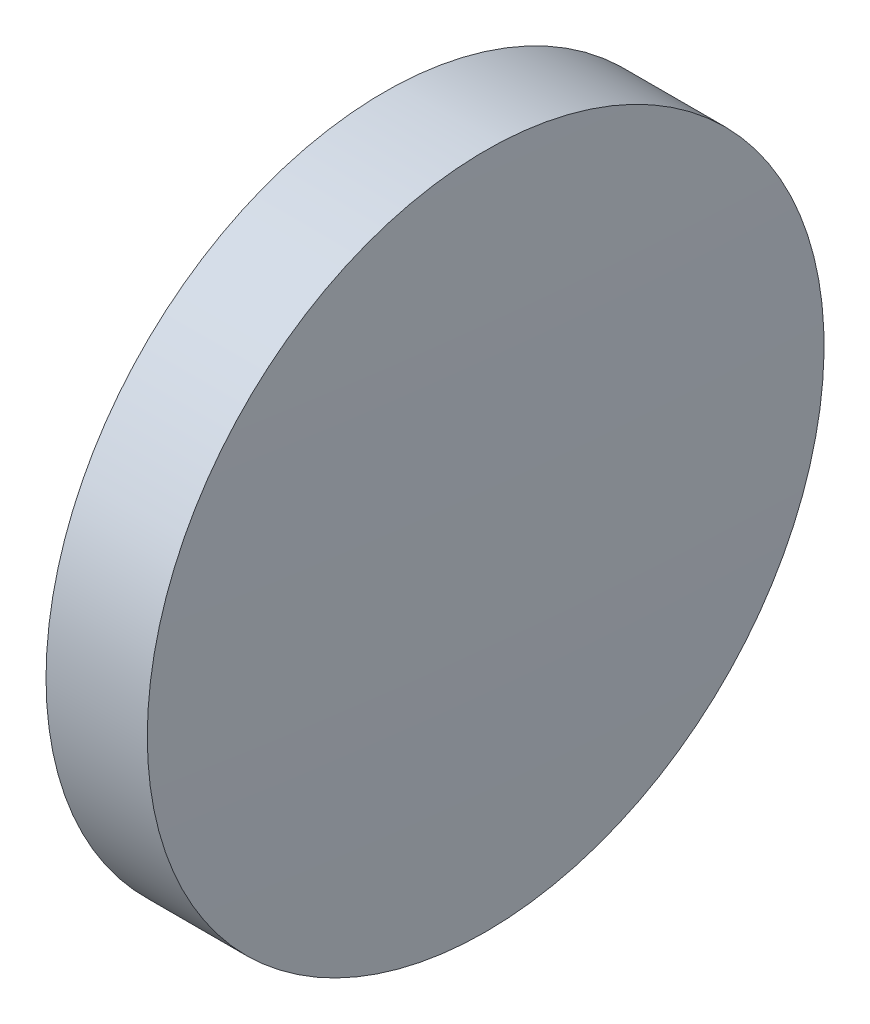
SolidWorks part; units mm, degrees
ref_plane "前视基准面" through (0, 0, 0) normal (0, 0, 1) x (1, 0, 0)
ref_plane "上视基准面" through (0, 0, 0) normal (0, 1, 0) x (1, 0, 0)
ref_plane "右视基准面" through (0, 0, 0) normal (1, 0, 0) x (0, 0, -1)
sketch "草图1" plane through (0, 0, 0) normal (0, 0, 1) x (1, 0, 0)
  line L0 (482.0826, 125.1785) -> (500.8786, 125.1785) construction
  line L1 (487.7125, 125.1785) -> (487.7125, 137.8785)
  line L2 (491.7125, 125.1785) -> (487.7125, 125.1785)
  line L5 (487.7125, 137.8785) -> (491.5125, 137.8785)
  arc A0 (491.7125, 125.1785) -> (491.5125, 137.8785) centre (88.3875, 125.1785) ccw
revolve "旋转1" add sketch "草图1" angle 360 about L0
